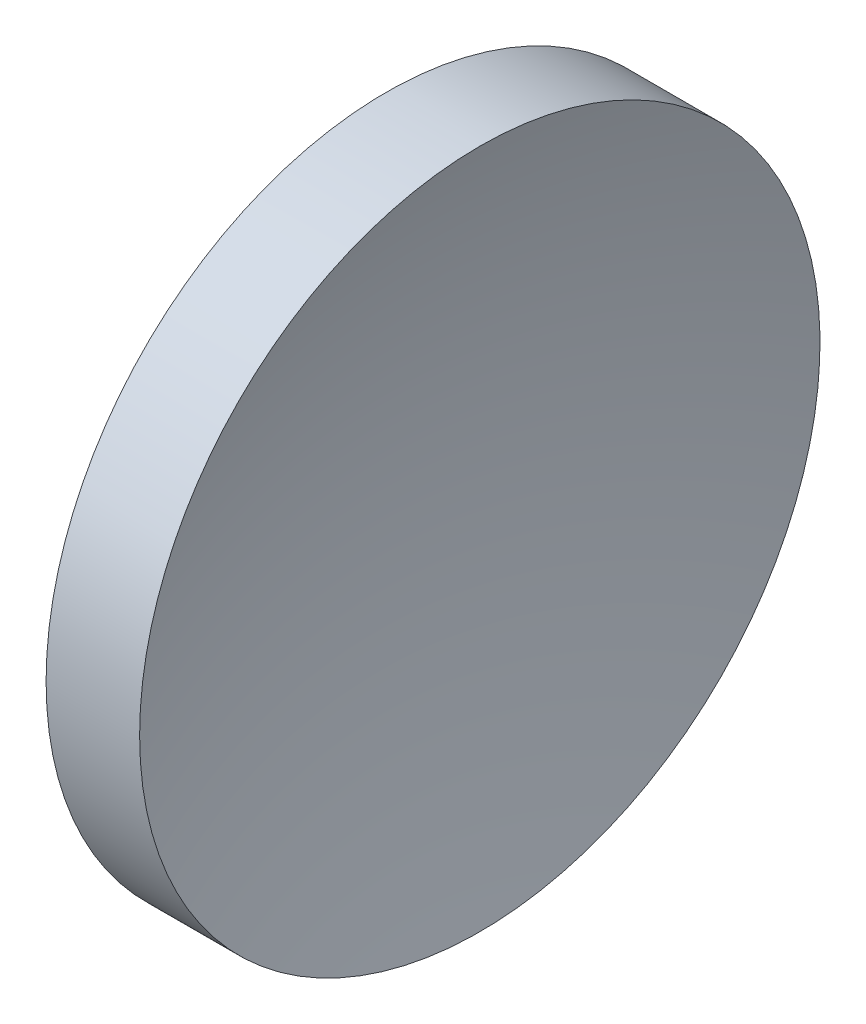
SolidWorks part; units mm, degrees
ref_plane "前视基准面" through (0, 0, 0) normal (0, 0, 1) x (1, 0, 0)
ref_plane "上视基准面" through (0, 0, 0) normal (0, 1, 0) x (1, 0, 0)
ref_plane "右视基准面" through (0, 0, 0) normal (1, 0, 0) x (0, 0, -1)
sketch "草图1" plane through (0, 0, 0) normal (0, 0, 1) x (1, 0, 0)
  line L0 (105.6218, 65.1556) -> (137.1869, 65.1556) construction
  line L1 (113.7394, 65.1556) -> (113.7394, 90.1556)
  line L2 (113.7394, 90.1556) -> (120.6126, 90.1556)
  line L3 (116.7394, 65.1556) -> (113.7394, 65.1556)
  arc A0 (120.6126, 90.1556) -> (116.7394, 65.1556) centre (199.3594, 65.1556) ccw
revolve "旋转1" add sketch "草图1" angle 360 about L0
